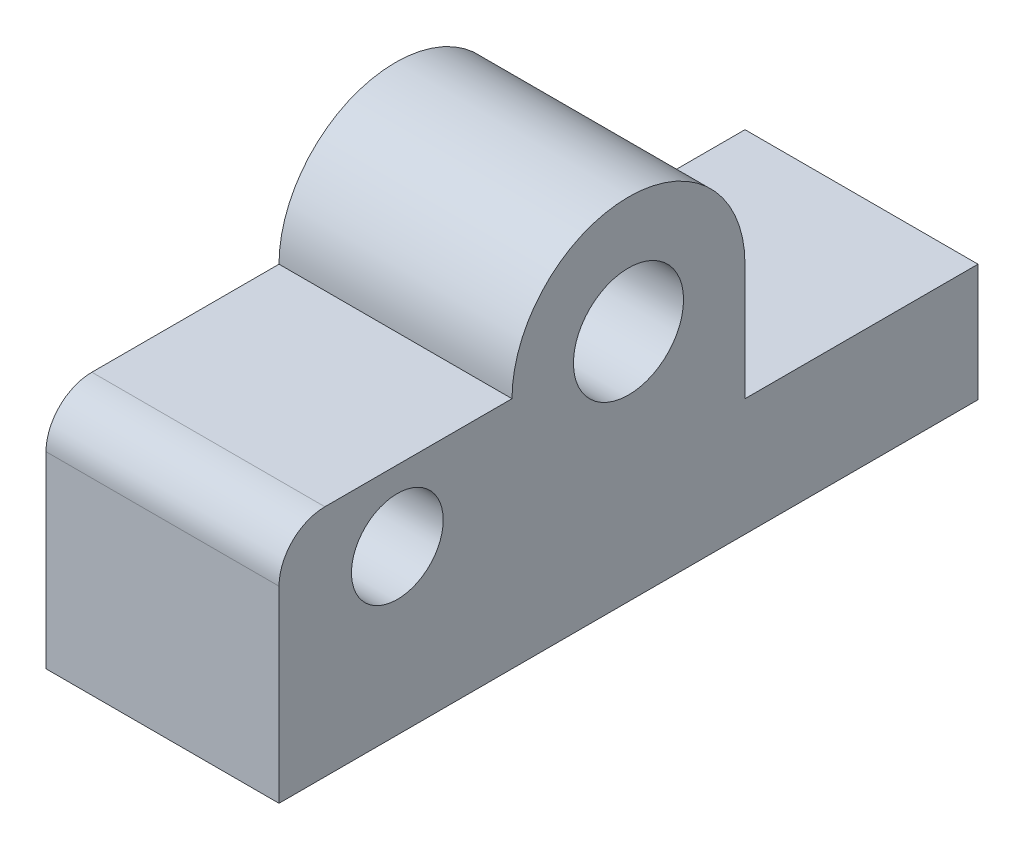
SolidWorks part; units mm, degrees
ref_plane "Front Plane" through (0, 0, 0) normal (0, 0, 1) x (1, 0, 0)
ref_plane "Top Plane" through (0, 0, 0) normal (0, 1, 0) x (1, 0, 0)
ref_plane "Right Plane" through (0, 0, 0) normal (1, 0, 0) x (0, 0, -1)
sketch "Sketch1" plane through (0, 0, 0) normal (1, 0, 0) x (0, 0, -1)
  line L0 (12.7, 0) -> (12.7, -12.7)
  line L1 (38.1, -12.7) -> (38.1, -25.5)
  line L2 (38.1, -25.5) -> (-38.1, -25.5)
  line L3 (-38.1, -25.5) -> (-38.1, -12.7)
  line L4 (12.7, -12.7) -> (38.1, -12.7)
  line L7 (-12.7, 0) -> (-38.1, 0)
  line L8 (-38.1, 0) -> (-38.1, -12.7)
  arc A0 (12.7, 0) -> (-12.7, 0) centre (0, 0) ccw
  dimension "D1" = 25.4
  dimension "D3" = 25.4
  dimension "D4" = 12.8
  dimension "D5" = 12.8
  dimension "D6" = 12.7
extrude "Boss-Extrude1" add sketch "Sketch1" along normal blind 25.4
sketch "Sketch2" plane through (25.4, 0, 0) normal (1, 0, 0) x (0, 0, -1)
  line L0 (38.1, -12.7) -> (12.7, -12.7) construction
  circle A0 centre (0, 0) radius 6
  circle A1 centre (-25.2, -7.7) radius 5
  dimension "D1" = 12
  dimension "D2" = 10
  dimension "D3" = 12.5
extrude "Cut-Extrude1" cut sketch "Sketch2" against normal through all
fillet "Fillet1" radius 5 1 edges at (12.7, 0, 38.1)
